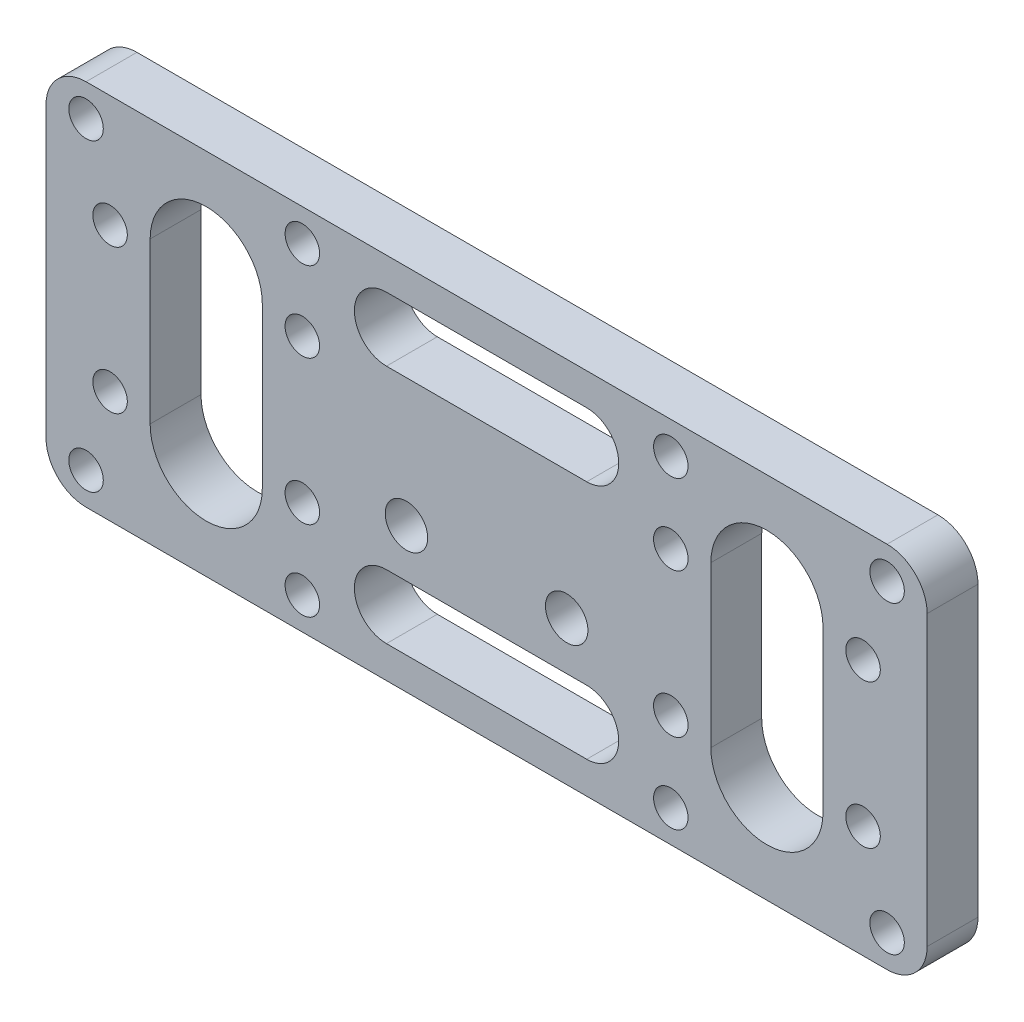
SolidWorks part; units mm, degrees
ref_plane "Front Plane" through (0, 0, 0) normal (0, 0, 1) x (1, 0, 0)
ref_plane "Top Plane" through (0, 0, 0) normal (0, 1, 0) x (1, 0, 0)
ref_plane "Right Plane" through (0, 0, 0) normal (1, 0, 0) x (0, 0, -1)
sketch "Sketch1" plane through (0, 0, 0) normal (0, 0, 1) x (1, 0, 0)
  line L0 (-55, -23) -> (-55, 23)
  line L1 (-55, -23) -> (55, -23)
  line L2 (-55, 23) -> (55, 23)
  line L3 (55, -23) -> (55, 23)
  line L4 (-55, -23) -> (55, 23) construction
  line L5 (-55, 23) -> (55, -23) construction
  point P1 (0, 0)
  dimension "D1" = 46
  dimension "D2" = 110
extrude "Boss-Extrude1" add sketch "Sketch1" along normal blind 6.35
sketch "Sketch2" plane through (0, 0, 6.35) normal (0, 0, 1) x (1, 0, 0)
  line L0 (-35, -10) -> (-35, 10) construction
  line L1 (-35, -10) -> (35, -10) construction
  line L2 (-35, 10) -> (35, 10) construction
  line L3 (35, -10) -> (35, 10) construction
  line L4 (-35, -10) -> (35, 10) construction
  line L5 (-35, 10) -> (35, -10) construction
  line L7 (-32.0555, 15.1) -> (-37.9445, 15.1)
  line L8 (-37.9445, 15.1) -> (-40.889, 10)
  line L9 (-40.889, 10) -> (-37.9445, 4.9)
  line L10 (-37.9445, 4.9) -> (-32.0555, 4.9)
  line L11 (-32.0555, 4.9) -> (-29.111, 10)
  line L12 (-29.111, 10) -> (-32.0555, 15.1)
  line L13 (37.9445, 15.1) -> (32.0555, 15.1)
  line L14 (32.0555, 15.1) -> (29.111, 10)
  line L15 (29.111, 10) -> (32.0555, 4.9)
  line L16 (32.0555, 4.9) -> (37.9445, 4.9)
  line L17 (37.9445, 4.9) -> (40.889, 10)
  line L18 (40.889, 10) -> (37.9445, 15.1)
  line L19 (37.9445, -4.9) -> (32.0555, -4.9)
  line L20 (32.0555, -4.9) -> (29.111, -10)
  line L21 (29.111, -10) -> (32.0555, -15.1)
  line L22 (32.0555, -15.1) -> (37.9445, -15.1)
  line L23 (37.9445, -15.1) -> (40.889, -10)
  line L24 (40.889, -10) -> (37.9445, -4.9)
  line L25 (-32.0555, -4.9) -> (-37.9445, -4.9)
  line L26 (-37.9445, -4.9) -> (-40.889, -10)
  line L27 (-40.889, -10) -> (-37.9445, -15.1)
  line L28 (-37.9445, -15.1) -> (-32.0555, -15.1)
  line L29 (-32.0555, -15.1) -> (-29.111, -10)
  line L30 (-29.111, -10) -> (-32.0555, -4.9)
  circle A0 centre (-35, 10) radius 5.1 construction
  circle A1 centre (35, 10) radius 5.1 construction
  circle A2 centre (35, -10) radius 5.1 construction
  circle A3 centre (-35, -10) radius 5.1 construction
  point P1 (0, 0)
  dimension "D1" = 70
  dimension "D2" = 20
  dimension "D3" = 10.2
  dimension "D4" = 2
  dimension "D5" = 2
extrude "Cut-Extrude1" [suppressed] cut sketch "Sketch2" against normal through all
sketch "Sketch4" plane through (0, 0, 0) normal (0, 0, -1) x (-1, 0, 0)
  line L1 (-47, 9) -> (-23, 9) construction
  line L2 (-47, 9) -> (-47, -9) construction
  line L3 (-47, -9) -> (-23, -9) construction
  line L4 (-23, 9) -> (-23, -9) construction
  line L5 (0, 23) -> (0, -23) construction
  line L6 (-55, 23) -> (55, 23) construction
  line L7 (55, -23) -> (-55, -23) construction
  line L8 (47, 9) -> (47, -9) construction
  line L9 (47, 9) -> (23, 9) construction
  line L10 (23, 9) -> (23, -9) construction
  line L11 (47, -9) -> (23, -9) construction
  point P4 (-23, 0)
  point P5 (-35, -9)
  point P20 (0, 0)
  dimension "D1" = 18
  dimension "D2" = 24
  dimension "D3" = 35
hole_wizard "#8 Clearance Hole2" positions "Sketch6" profile "Sketch5" hole size "#8" standard "ANSI Inch" end condition through all
sketch "Sketch6" plane through (0, 0, 0) normal (0, 0, -1) x (-1, 0, 0)
  point P0 (-47, 9)
  point P3 (-23, 9)
  point P6 (-23, -9)
  point P9 (-47, -9)
  point P12 (23, -9)
  point P15 (23, 9)
  point P18 (47, 9)
  point P21 (47, -9)
sketch "Sketch5" plane through (47, 9, 0) normal (1, 0, 0) x (0, 1, 0)
  line L0 (0, 0) -> (0, 6.35)
  line L1 (0, 6.35) -> (2.1526, 6.35)
  line L2 (2.1526, 6.35) -> (2.1526, 0)
  line L5 (2.1526, 0) -> (0, 0)
  line L11 (0, -6.35) -> (0, 107.95) construction
  dimension "Thru Hole Dia." = 4.3053
  dimension "Thru Hole Depth" = 6.35
fillet "Fillet1" radius 5 4 edges at (-55, 23, 3.175) (-55, -23, 3.175) (55, -23, 3.175) (55, 23, 3.175)
sketch "Sketch7" plane through (0, 0, 6.35) normal (0, 0, 1) x (1, 0, 0)
  line L0 (-10, -5) -> (10, -5) construction
  point P0 (0, 0)
  point P4 (0, -5)
  dimension "D1" = 20
  dimension "D2" = 5
hole_wizard "M5 Clearance Hole1" positions "Sketch9" profile "Sketch8" hole size "M5" standard "ANSI Metric" end condition through all
sketch "Sketch9" plane through (0, 0, 6.35) normal (0, 0, 1) x (1, 0, 0)
  point P0 (-10, -5)
  point P3 (10, -5)
sketch "Sketch8" plane through (-10, -5, 6.35) normal (1, 0, 0) x (0, -1, 0)
  line L0 (0, 0) -> (0, 6.35)
  line L1 (0, 6.35) -> (2.65, 6.35)
  line L2 (2.65, 6.35) -> (2.65, 0)
  line L5 (2.65, 0) -> (0, 0)
  line L11 (0, -6.35) -> (0, 107.95) construction
  dimension "Thru Hole Dia." = 5.3
  dimension "Thru Hole Depth" = 6.35
sketch "Sketch10" plane through (0, 0, 6.35) normal (0, 0, 1) x (1, 0, 0)
  line L1 (-23, -19) -> (23, -19) construction
  line L2 (-23, -19) -> (-23, 19) construction
  line L3 (-23, 19) -> (23, 19) construction
  line L4 (23, -19) -> (23, 19) construction
  line L5 (-23, -19) -> (23, 19) construction
  line L6 (-23, 19) -> (23, -19) construction
  line L7 (-50, -19) -> (50, -19) construction
  line L8 (-50, -19) -> (-50, 19) construction
  line L9 (-50, 19) -> (50, 19) construction
  line L10 (50, -19) -> (50, 19) construction
  line L11 (-50, -19) -> (50, 19) construction
  line L12 (-50, 19) -> (50, -19) construction
  point P0 (0, 0)
  point P6 (0, 0)
  dimension "D1" = 46
  dimension "D2" = 38
  dimension "D3" = 38
  dimension "D4" = 100
hole_wizard "#8 Clearance Hole1" positions "Sketch12" profile "Sketch11" hole size "#8" standard "ANSI Inch" end condition through all
sketch "Sketch12" plane through (0, 0, 6.35) normal (0, 0, 1) x (1, 0, 0)
  point P0 (-23, 19)
  point P3 (-23, -19)
  point P6 (23, -19)
  point P9 (23, 19)
  point P13 (-50, 19)
  point P16 (-50, -19)
  point P19 (50, -19)
  point P22 (50, 19)
sketch "Sketch11" plane through (-23, 19, 6.35) normal (1, 0, 0) x (0, -1, 0)
  line L0 (0, 0) -> (0, 6.35)
  line L1 (0, 6.35) -> (2.1526, 6.35)
  line L2 (2.1526, 6.35) -> (2.1526, 0)
  line L5 (2.1526, 0) -> (0, 0)
  line L11 (0, -6.35) -> (0, 107.95) construction
  dimension "Thru Hole Dia." = 4.3053
  dimension "Thru Hole Depth" = 6.35
sketch "Sketch13" plane through (0, 0, 6.35) normal (0, 0, 1) x (1, 0, 0)
  line L0 (35, 10) -> (35, -10) construction
  line L1 (42, 10) -> (42, -10)
  line L2 (28, 10) -> (28, -10)
  line L3 (47, -9) -> (23, 9) construction
  line L4 (47, 9) -> (23, -9) construction
  line L5 (0, -23) -> (0, 23) construction
  line L6 (-50, -23) -> (50, -23) construction
  line L7 (50, 23) -> (-50, 23) construction
  line L8 (-35, 10) -> (-35, -10) construction
  line L9 (-42, 10) -> (-42, -10)
  line L10 (-28, 10) -> (-28, -10)
  arc A0 (42, 10) -> (28, 10) centre (35, 10) ccw
  arc A1 (28, -10) -> (42, -10) centre (35, -10) ccw
  circle A2 centre (47, 9) radius 2.1526 construction
  circle A3 centre (23, -9) radius 2.1526 construction
  circle A4 centre (23, 9) radius 2.1526 construction
  circle A5 centre (47, -9) radius 2.1526 construction
  circle A6 centre (47, 9) radius 2.1527
  circle A7 centre (23, -9) radius 2.1527
  circle A8 centre (23, 9) radius 2.1527
  circle A9 centre (47, -9) radius 2.1527
  arc A10 (-42, 10) -> (-28, 10) centre (-35, 10) cw
  arc A11 (-28, -10) -> (-42, -10) centre (-35, -10) cw
  point P2 (35, 0)
  point P7 (35, 0)
  point P29 (-35, 0)
  dimension "D1" = 20
  dimension "D2" = 14
extrude "Cut-Extrude2" cut sketch "Sketch13" against normal blind 10
sketch "Sketch14" plane through (0, 0, 6.35) normal (0, 0, 1) x (1, 0, 0)
  line L0 (-12.5, -15) -> (12.5, -15) construction
  line L1 (-12.5, -11) -> (12.5, -11)
  line L2 (-12.5, -19) -> (12.5, -19)
  line L3 (-12.5, 15) -> (12.5, 15) construction
  line L4 (-12.5, 19) -> (12.5, 19)
  line L7 (-12.5, 11) -> (12.5, 11)
  line L10 (-50, -23) -> (50, -23) construction
  line L11 (50, 23) -> (-50, 23) construction
  arc A0 (-12.5, -11) -> (-12.5, -19) centre (-12.5, -15) ccw
  arc A1 (12.5, -19) -> (12.5, -11) centre (12.5, -15) ccw
  arc A4 (-12.5, 19) -> (-12.5, 11) centre (-12.5, 15) ccw
  arc A5 (12.5, 11) -> (12.5, 19) centre (12.5, 15) ccw
  point P2 (0, -15)
  point P11 (0, 15)
  point P16 (0, 0)
  dimension "D1" = 8
  dimension "D2" = 8
  dimension "D3" = 8
  dimension "D4" = 25
  dimension "D5" = 8
extrude "Cut-Extrude3" cut sketch "Sketch14" against normal through all
